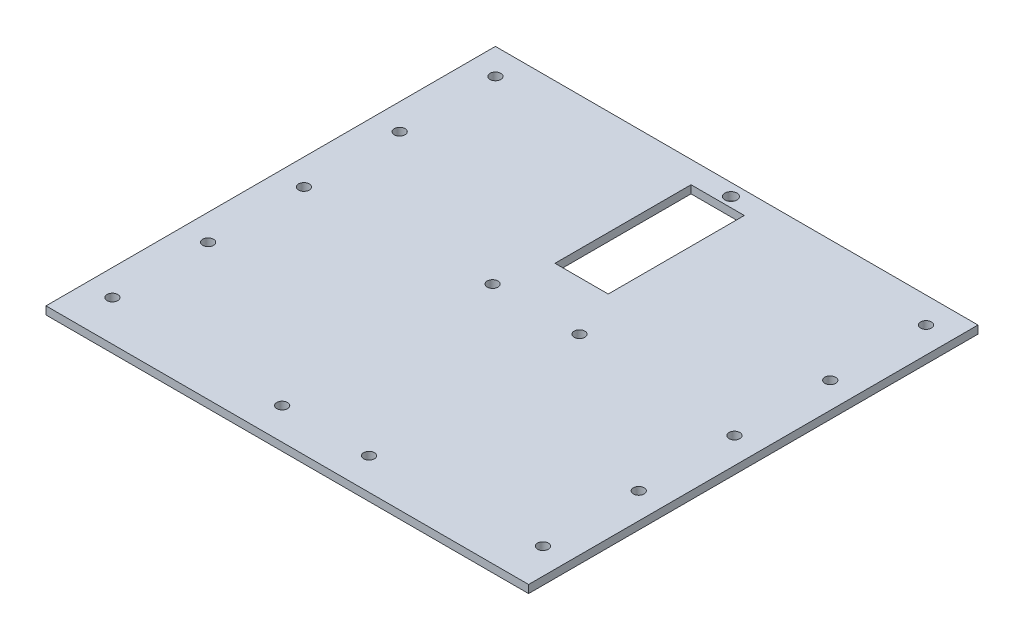
SolidWorks part; units mm, degrees
ref_plane "Front Plane" through (0, 0, 0) normal (0, 0, 1) x (1, 0, 0)
ref_plane "Top Plane" through (0, 0, 0) normal (0, 1, 0) x (1, 0, 0)
ref_plane "Right Plane" through (0, 0, 0) normal (1, 0, 0) x (0, 0, -1)
sketch "Sketch1" plane through (0, 0, 0) normal (0, 1, 0) x (1, 0, 0)
  line L1 (96.647, -90) -> (-96.647, -90)
  line L2 (96.647, -90) -> (96.647, 90)
  line L3 (96.647, 90) -> (-96.647, 90)
  line L4 (-96.647, -90) -> (-96.647, 90)
  line L5 (96.647, -90) -> (-96.647, 90) construction
  line L6 (96.647, 90) -> (-96.647, -90) construction
  point P0 (0, 0)
  dimension "D1" = 193.294
  dimension "D2" = 180
extrude "Boss-Extrude1" add sketch "Sketch1" along normal blind 3.175
sketch "Sketch2" plane through (0, 3.175, 0) normal (0, 1, 0) x (1, 0, 0)
  line L0 (-96.647, 90) -> (-96.647, -90) construction
  line L1 (96.647, 90) -> (-96.647, 90) construction
  line L2 (-96.647, -90) -> (96.647, -90) construction
  circle A0 centre (-86.233, 79.586) radius 2.159
  circle A1 centre (86.233, 79.586) radius 2.159
  circle A2 centre (86.233, 41.232) radius 2.159
  circle A3 centre (86.233, 2.878) radius 2.159
  circle A4 centre (86.233, -35.476) radius 2.159
  circle A5 centre (-86.233, 41.232) radius 2.159
  circle A6 centre (-86.233, 2.878) radius 2.159
  circle A7 centre (-86.233, -35.476) radius 2.159
  circle A8 centre (-86.233, -73.83) radius 2.159
  circle A9 centre (86.233, -73.83) radius 2.159
  dimension "D2" = 4.318
  dimension "D3" = 10.414
  dimension "D1" = 10.414
  dimension "D4" = 2
  dimension "D5" = 5
extrude "Cut-Extrude1" cut sketch "Sketch2" against normal through all
sketch "Sketch3" plane through (0, 3.175, 0) normal (0, 1, 0) x (1, 0, 0)
  circle A0 centre (-14.7644, 7.0022) radius 2.159
  circle A1 centre (20.0336, 7.0022) radius 2.159
  circle A2 centre (20.0336, -77.3) radius 2.159
  circle A3 centre (-14.7644, -77.3) radius 2.159
  circle A4 centre (2.6036, 85.0801) radius 2.4153
extrude "Cut-Extrude2" cut sketch "Sketch3" against normal through all
sketch "Sketch4" plane through (0, 3.175, 0) normal (0, 1, 0) x (1, 0, 0)
  line L1 (-9.4788, 81.1915) -> (11.8516, 81.1915)
  line L2 (-9.4788, 81.1915) -> (-9.4788, 26.6912)
  line L3 (-9.4788, 26.6912) -> (11.8516, 26.6912)
  line L4 (11.8516, 81.1915) -> (11.8516, 26.6912)
extrude "Cut-Extrude3" cut sketch "Sketch4" against normal through all
